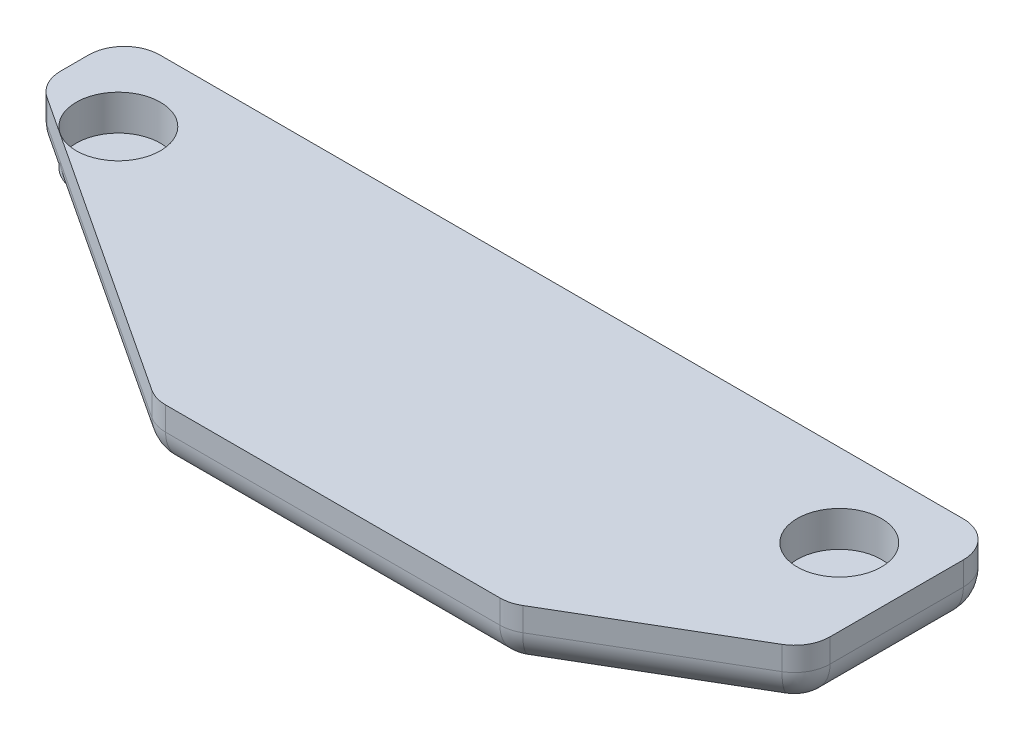
SolidWorks part; units mm, degrees
ref_plane "Front Plane" through (0, 0, 0) normal (0, 0, 1) x (1, 0, 0)
ref_plane "Top Plane" through (0, 0, 0) normal (0, 1, 0) x (1, 0, 0)
ref_plane "Right Plane" through (0, 0, 0) normal (1, 0, 0) x (0, 0, -1)
sketch "Sketch2" plane through (0, 0, 0) normal (0, 1, 0) x (1, 0, 0)
  line L0 (-21.2162, 11.7419) -> (-21.2162, 8.2419)
  line L1 (-21.2162, 8.2419) -> (-7.2162, -0.9581)
  line L2 (-7.2162, -0.9581) -> (7.7838, -0.9581)
  line L3 (7.7838, -0.9581) -> (15.7838, 3.7419)
  line L4 (15.7838, 3.7419) -> (15.7838, 11.7419)
  line L7 (-21.2162, 11.7419) -> (15.7838, 11.7419)
  dimension "D1" = 37
  dimension "D2" = 12.7
  dimension "D3" = 15
  dimension "D4" = 8
  dimension "D5" = 3.5
  dimension "D6" = 8
extrude "Boss-Extrude1" add sketch "Sketch2" along normal blind 2.5
sketch "Sketch4" plane through (0, 2.5, 0) normal (0, 1, 0) x (1, 0, 0)
  line L0 (-17.9662, 11.241) -> (-17.9662, -1.2869) construction
  line L1 (-21.2162, 8.2419) -> (15.7838, 8.2419) construction
  line L2 (-21.2162, 11.7419) -> (-21.2162, 8.2419) construction
  line L3 (15.7838, 11.7419) -> (-21.2162, 11.7419) construction
  line L4 (-2.7162, 11.7419) -> (-2.7162, -0.9581) construction
  line L5 (-7.2162, -0.9581) -> (7.7838, -0.9581) construction
  line L6 (12.5338, 11.241) -> (12.5338, -1.2869) construction
  circle A0 centre (-17.9662, 8.2419) radius 1.78
  circle A1 centre (12.5338, 8.2419) radius 1.78
  point P15 (-2.7162, 8.2419)
  dimension "D1" = 3.25
  dimension "D2" = 3.5
extrude "Cut-Extrude1" cut sketch "Sketch4" against normal blind 1.5
fillet "Fillet1" radius 1.5 12 edges at (7.7838, 1.25, 0.9581) (-7.2162, 1.25, 0.9581) (-21.2162, 0, -9.9919) (-14.2162, 0, -3.6419) (0.2838, 0, 0.9581) (11.7838, 0, -1.3919) (15.7838, 1.25, -3.7419) (15.7838, 0, -7.7419) (-2.7162, 0, -11.7419) (15.7838, 1.25, -11.7419) (-21.2162, 1.25, -8.2419) (-21.2162, 1.25, -11.7419)
